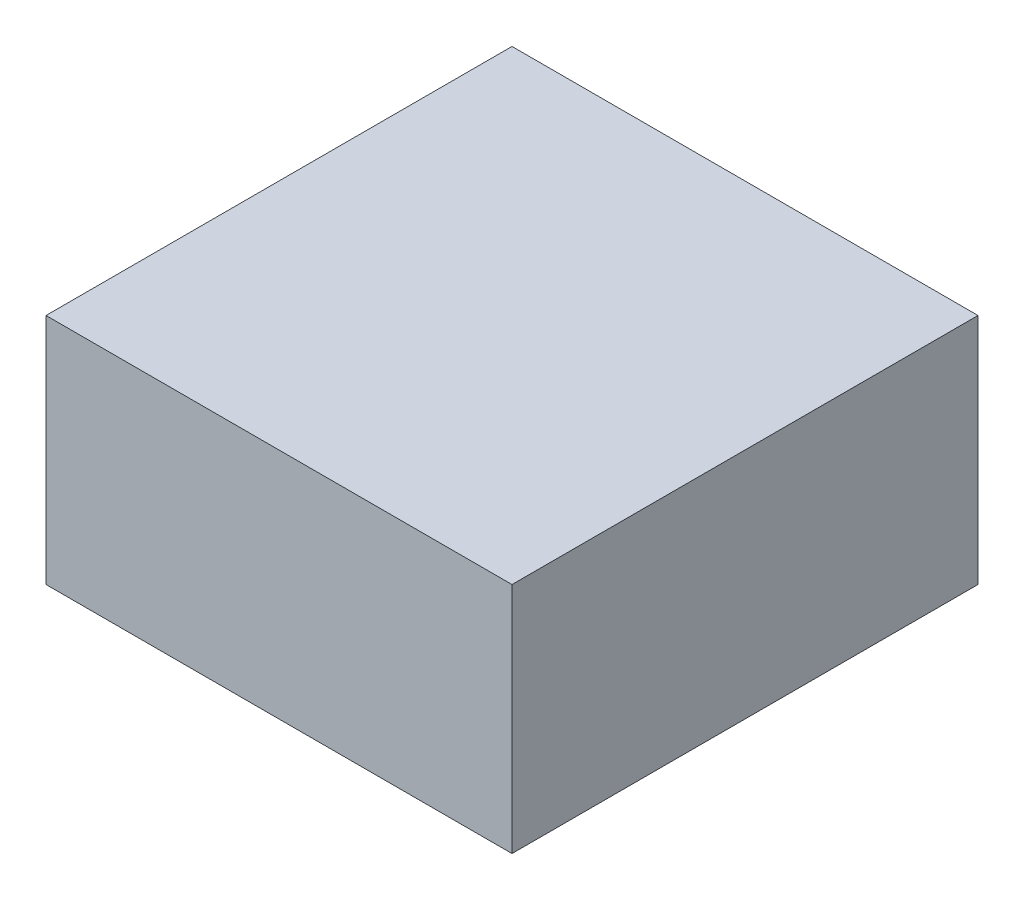
SolidWorks part; units mm, degrees
ref_plane "前视基准面" through (0, 0, 0) normal (0, 0, 1) x (1, 0, 0)
ref_plane "上视基准面" through (0, 0, 0) normal (0, 1, 0) x (1, 0, 0)
ref_plane "右视基准面" through (0, 0, 0) normal (1, 0, 0) x (0, 0, -1)
sketch "草图1" plane through (0, 0, 0) normal (0, 1, 0) x (1, 0, 0)
  line L1 (0, 0) -> (40, 0)
  line L2 (0, 0) -> (0, 40)
  line L3 (0, 40) -> (40, 40)
  line L4 (40, 0) -> (40, 40)
  dimension "D1" = 40
  dimension "D2" = 40
extrude "凸台-拉伸2" add sketch "草图1" along normal blind 20 contours L2 L3 L4 L1
sketch "草图2" plane through (0, 0, 0) normal (-1, 0, 0) x (0, 0, 1)
  line L0 (-40, 10) -> (0, 10) construction
  line L1 (-40, 20) -> (-40, 0) construction
  line L2 (0, 20) -> (0, 0) construction
  line L4 (-36, 16) -> (-4, 16)
  line L5 (-36, 16) -> (-36, 4)
  line L6 (-36, 4) -> (-4, 4)
  line L7 (-4, 16) -> (-4, 4)
  point P10 (-20, 10)
  point P13 (-20, 4)
  dimension "D1" = 16
  dimension "D2" = 12
  dimension "D3" = 32
  dimension "D4" = 6
extrude "切除-拉伸1" cut sketch "草图2" against normal blind 20 contours L5 L0 L7 L4 | L0 L5 L6 L7
ref_point "点1"
